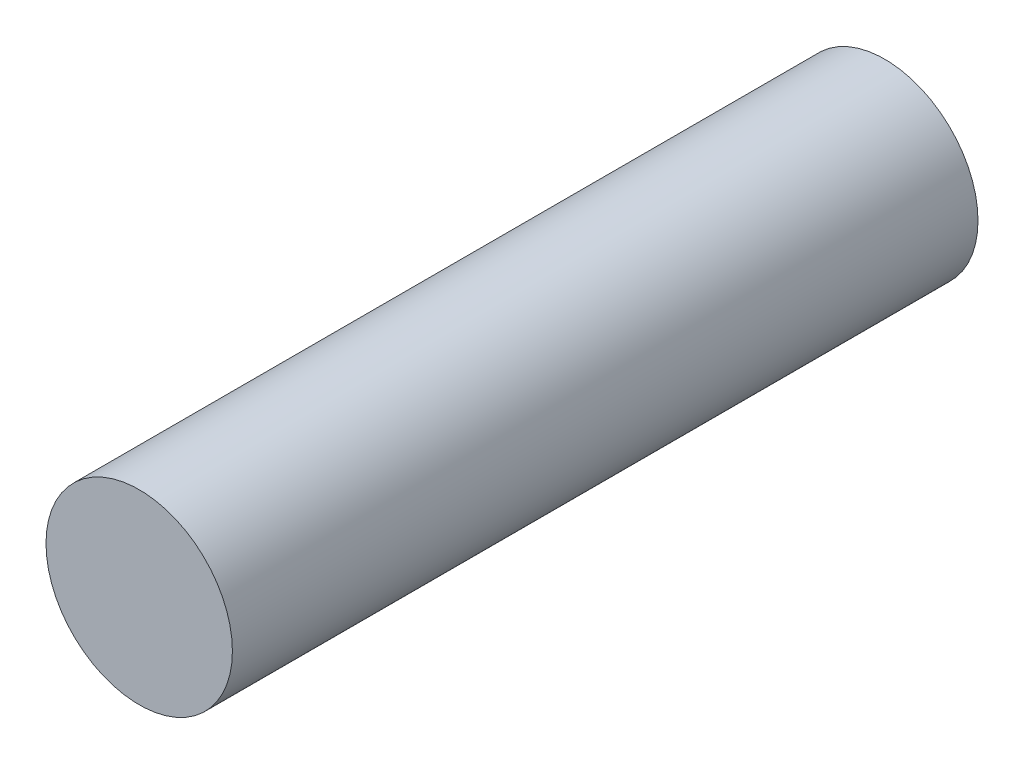
SolidWorks part; units mm, degrees
ref_plane "Front Plane" through (0, 0, 0) normal (0, 0, 1) x (1, 0, 0)
ref_plane "Top Plane" through (0, 0, 0) normal (0, 1, 0) x (1, 0, 0)
ref_plane "Right Plane" through (0, 0, 0) normal (1, 0, 0) x (0, 0, -1)
sketch "Sketch1" plane through (0, 0, 0) normal (0, 0, 1) x (1, 0, 0)
  circle A0 centre (0, 0) radius 4.7625
  dimension "D1" = 9.525
extrude "Boss-Extrude1" add sketch "Sketch1" along normal blind 38.1
